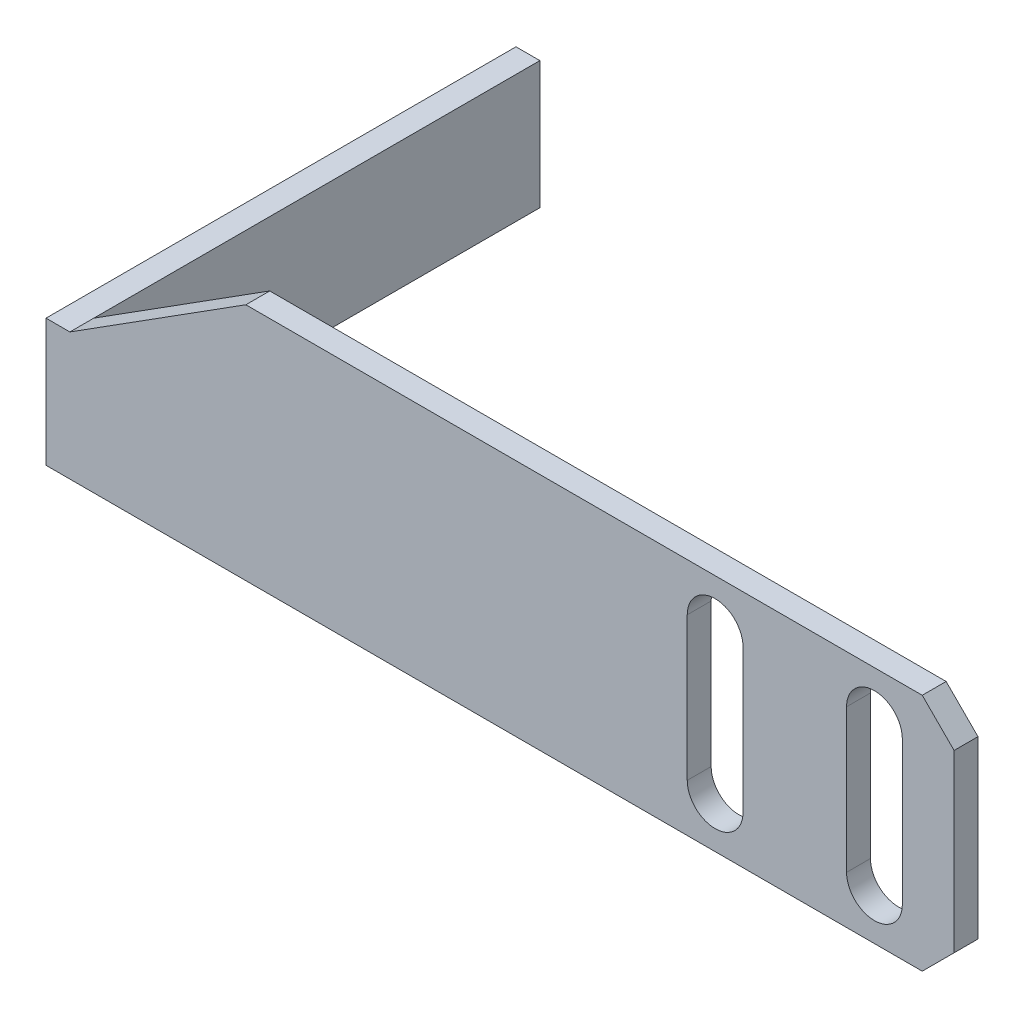
SolidWorks part; units mm, degrees
ref_plane "Front Plane" through (0, 0, 0) normal (0, 0, 1) x (1, 0, 0)
ref_plane "Top Plane" through (0, 0, 0) normal (0, 1, 0) x (1, 0, 0)
ref_plane "Right Plane" through (0, 0, 0) normal (1, 0, 0) x (0, 0, -1)
sketch "Sketch4" plane through (0, 0, 0) normal (0, 0, 1) x (1, 0, 0)
  line L1 (-21.8182, -18.75) -> (35.1818, -18.75)
  line L2 (-21.8182, -18.75) -> (-21.8182, -10.75)
  line L3 (-9.2727, -3.75) -> (35.1818, -3.75)
  line L4 (35.1818, -18.75) -> (35.1818, -3.75)
  line L5 (-21.8182, -10.75) -> (-20.3182, -10.75)
  line L6 (-20.3182, -10.75) -> (-9.2727, -3.75)
  dimension "D1" = 57
  dimension "D2" = 15
  dimension "D3" = 8
  dimension "D4" = 1.5
extrude "Boss-Extrude2" add sketch "Sketch4" along normal blind 1.5
sketch "Sketch5" plane through (0, 0, 0) normal (0, 0, -1) x (-1, 0, 0)
  line L1 (21.8182, -18.75) -> (-35.1818, -18.75) construction
  line L2 (21.8182, -10.75) -> (20.3182, -10.75)
  line L3 (21.8182, -10.75) -> (21.8182, -18.75)
  line L4 (21.8182, -18.75) -> (20.3182, -18.75)
  line L5 (20.3182, -10.75) -> (20.3182, -18.75)
  dimension "D1" = 1.5
extrude "Boss-Extrude3" add sketch "Sketch5" along normal blind 28
sketch "Sketch6" plane through (0, 0, 1.5) normal (0, 0, 1) x (1, 0, 0)
  line L2 (18.4318, -6.75) -> (18.4318, -15.75)
  line L4 (21.9318, -6.75) -> (21.9318, -15.75)
  line L6 (28.4318, -6.75) -> (28.4318, -15.75)
  line L8 (31.9318, -6.75) -> (31.9318, -15.75)
  arc A0 (21.9318, -6.75) -> (18.4318, -6.75) centre (20.1818, -6.75) ccw
  arc A1 (18.4318, -15.75) -> (21.9318, -15.75) centre (20.1818, -15.75) ccw
  arc A2 (31.9318, -6.75) -> (28.4318, -6.75) centre (30.1818, -6.75) ccw
  arc A3 (28.4318, -15.75) -> (31.9318, -15.75) centre (30.1818, -15.75) ccw
  dimension "D1" = 3.5
  dimension "D2" = 3.5
  dimension "D5" = 9
  dimension "D6" = 9
extrude "Cut-Extrude1" cut sketch "Sketch6" against normal blind 28
chamfer "Chamfer1" distance 2 angle 45 2 edges at (35.1818, -18.75, 0.75) (35.1818, -3.75, 0.75)
